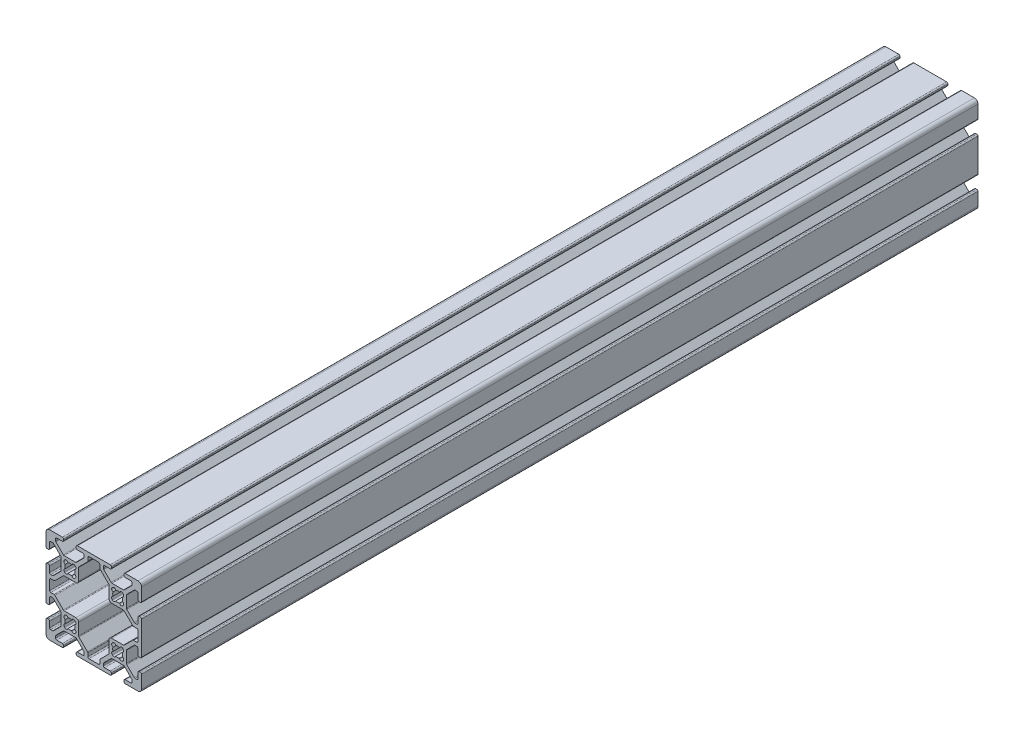
SolidWorks part; units mm, degrees
material "6105-T5 Aluminum"
ref_plane "Front Plane" through (0, 0, 0) normal (0, 0, 1) x (1, 0, 0)
ref_plane "Top Plane" through (0, 0, 0) normal (0, 1, 0) x (1, 0, 0)
ref_plane "Right Plane" through (0, 0, 0) normal (1, 0, 0) x (0, 0, -1)
sketch "Sketch1" plane through (0, 0, 0) normal (0, 0, 1) x (1, 0, 0)
  line L0 (-2.1249, 17.6955) -> (-2.3045, 17.8751)
  line L1 (-2.3045, 22.1249) -> (-2.1249, 22.3045)
  line L2 (2.1249, 22.3045) -> (2.3045, 22.1249)
  line L3 (2.3045, 17.8751) -> (2.1249, 17.6955)
  line L4 (-22.1249, 17.6955) -> (-22.3045, 17.8751)
  line L5 (-22.3045, 22.1249) -> (-22.1249, 22.3045)
  line L6 (-17.8751, 22.3045) -> (-17.6955, 22.1249)
  line L7 (-17.6955, 17.8751) -> (-17.8751, 17.6955)
  line L8 (-2.1249, -2.3045) -> (-2.3045, -2.1249)
  line L9 (-2.3045, 2.1249) -> (-2.1249, 2.3045)
  line L10 (2.1249, 2.3045) -> (2.3045, 2.1249)
  line L11 (2.3045, -2.1249) -> (2.1249, -2.3045)
  line L12 (-12.505, -7.992) -> (-12.505, -6.6448)
  line L13 (-12.6538, -6.2856) -> (-16.1962, -2.7431)
  line L14 (-16.345, -2.3839) -> (-16.345, 2.512)
  line L15 (-17.488, 3.655) -> (-22.3839, 3.655)
  line L16 (-22.7431, 3.8038) -> (-26.2856, 7.3462)
  line L17 (-26.6448, 7.495) -> (-27.992, 7.495)
  line L18 (-28.5, 8.003) -> (-28.5, 11.997)
  line L19 (-27.992, 12.505) -> (-26.6448, 12.505)
  line L20 (-26.2856, 12.6538) -> (-22.7431, 16.1962)
  line L21 (-22.3839, 16.345) -> (-17.488, 16.345)
  line L22 (-16.345, 17.488) -> (-16.345, 22.3839)
  line L23 (-16.1962, 22.7431) -> (-12.6538, 26.2856)
  line L24 (-12.505, 26.6448) -> (-12.505, 27.992)
  line L25 (-11.997, 28.5) -> (-8.003, 28.5)
  line L26 (-7.495, 27.992) -> (-7.495, 26.6448)
  line L27 (-7.3462, 26.2856) -> (-3.8038, 22.7431)
  line L28 (-3.655, 22.3839) -> (-3.655, 17.488)
  line L29 (-2.512, 16.345) -> (2.3839, 16.345)
  line L30 (2.7431, 16.1962) -> (6.2856, 12.6538)
  line L31 (6.6448, 12.505) -> (7.992, 12.505)
  line L32 (8.5, 11.997) -> (8.5, 8.003)
  line L33 (7.992, 7.495) -> (6.6448, 7.495)
  line L34 (6.2856, 7.3462) -> (2.7431, 3.8038)
  line L35 (2.3839, 3.655) -> (-2.512, 3.655)
  line L36 (-3.655, 2.512) -> (-3.655, -2.3839)
  line L37 (-3.8038, -2.7431) -> (-7.3462, -6.2856)
  line L38 (-7.495, -6.6448) -> (-7.495, -7.992)
  line L39 (-8.003, -8.5) -> (-11.997, -8.5)
  line L40 (-22.1249, -2.3045) -> (-22.3045, -2.1249)
  line L41 (-22.3045, 2.1249) -> (-22.1249, 2.3045)
  line L42 (-17.8751, 2.3045) -> (-17.6955, 2.1249)
  line L43 (-17.6955, -2.1249) -> (-17.8751, -2.3045)
  line L44 (-22.3839, -3.655) -> (-17.6161, -3.655)
  line L45 (-17.2569, -3.8038) -> (-14.1538, -6.9069)
  line L46 (-14.005, -7.2661) -> (-14.005, -7.992)
  line L47 (-14.513, -8.5) -> (-16.862, -8.5)
  line L48 (-17.37, -9.008) -> (-17.37, -9.492)
  line L49 (-16.862, -10) -> (-3.138, -10)
  line L50 (-2.63, -9.492) -> (-2.63, -9.008)
  line L51 (-3.138, -8.5) -> (-5.487, -8.5)
  line L52 (-5.995, -7.992) -> (-5.995, -7.2661)
  line L53 (-5.8462, -6.9069) -> (-2.7431, -3.8038)
  line L54 (-2.3839, -3.655) -> (2.3839, -3.655)
  line L55 (2.7431, -3.8038) -> (5.8462, -6.9069)
  line L56 (5.995, -7.2661) -> (5.995, -7.992)
  line L57 (5.487, -8.5) -> (3.138, -8.5)
  line L58 (2.63, -9.008) -> (2.63, -9.492)
  line L59 (3.138, -10) -> (8.5, -10)
  line L60 (10, -8.5) -> (10, -3.138)
  line L61 (9.492, -2.63) -> (9.008, -2.63)
  line L62 (8.5, -3.138) -> (8.5, -5.487)
  line L63 (7.992, -5.995) -> (7.2661, -5.995)
  line L64 (6.9069, -5.8462) -> (3.8038, -2.7431)
  line L65 (3.655, -2.3839) -> (3.655, 2.3839)
  line L66 (3.8038, 2.7431) -> (6.9069, 5.8462)
  line L67 (7.2661, 5.995) -> (7.992, 5.995)
  line L68 (8.5, 5.487) -> (8.5, 3.138)
  line L69 (9.008, 2.63) -> (9.492, 2.63)
  line L70 (10, 3.138) -> (10, 16.862)
  line L71 (9.492, 17.37) -> (9.008, 17.37)
  line L72 (8.5, 16.862) -> (8.5, 14.513)
  line L73 (7.992, 14.005) -> (7.2661, 14.005)
  line L74 (6.9069, 14.1538) -> (3.8038, 17.2569)
  line L75 (3.655, 17.6161) -> (3.655, 22.3839)
  line L76 (3.8038, 22.7431) -> (6.9069, 25.8462)
  line L77 (7.2661, 25.995) -> (7.992, 25.995)
  line L78 (8.5, 25.487) -> (8.5, 23.138)
  line L79 (9.008, 22.63) -> (9.492, 22.63)
  line L80 (10, 23.138) -> (10, 28.5)
  line L81 (8.5, 30) -> (3.138, 30)
  line L82 (2.63, 29.492) -> (2.63, 29.008)
  line L83 (3.138, 28.5) -> (5.487, 28.5)
  line L84 (5.995, 27.992) -> (5.995, 27.2661)
  line L85 (5.8462, 26.9069) -> (2.7431, 23.8038)
  line L86 (2.3839, 23.655) -> (-2.3839, 23.655)
  line L87 (-2.7431, 23.8038) -> (-5.8462, 26.9069)
  line L88 (-5.995, 27.2661) -> (-5.995, 27.992)
  line L89 (-5.487, 28.5) -> (-3.138, 28.5)
  line L90 (-2.63, 29.008) -> (-2.63, 29.492)
  line L91 (-3.138, 30) -> (-16.862, 30)
  line L92 (-17.37, 29.492) -> (-17.37, 29.008)
  line L93 (-16.862, 28.5) -> (-14.513, 28.5)
  line L94 (-14.005, 27.992) -> (-14.005, 27.2661)
  line L95 (-14.1538, 26.9069) -> (-17.2569, 23.8038)
  line L96 (-17.6161, 23.655) -> (-22.3839, 23.655)
  line L97 (-22.7431, 23.8038) -> (-25.8462, 26.9069)
  line L98 (-25.995, 27.2661) -> (-25.995, 27.992)
  line L99 (-25.487, 28.5) -> (-23.138, 28.5)
  line L100 (-22.63, 29.008) -> (-22.63, 29.492)
  line L101 (-23.138, 30) -> (-28.5, 30)
  line L102 (-30, 28.5) -> (-30, 23.138)
  line L103 (-29.492, 22.63) -> (-29.008, 22.63)
  line L104 (-28.5, 23.138) -> (-28.5, 25.487)
  line L105 (-27.992, 25.995) -> (-27.2661, 25.995)
  line L106 (-26.9069, 25.8462) -> (-23.8038, 22.7431)
  line L107 (-23.655, 22.3839) -> (-23.655, 17.6161)
  line L108 (-23.8038, 17.2569) -> (-26.9069, 14.1538)
  line L109 (-27.2661, 14.005) -> (-27.992, 14.005)
  line L110 (-28.5, 14.513) -> (-28.5, 16.862)
  line L111 (-29.008, 17.37) -> (-29.492, 17.37)
  line L112 (-30, 16.862) -> (-30, 3.138)
  line L113 (-29.492, 2.63) -> (-29.008, 2.63)
  line L114 (-28.5, 3.138) -> (-28.5, 5.487)
  line L115 (-27.992, 5.995) -> (-27.2661, 5.995)
  line L116 (-26.9069, 5.8462) -> (-23.8038, 2.7431)
  line L117 (-23.655, 2.3839) -> (-23.655, -2.3839)
  line L118 (-23.8038, -2.7431) -> (-26.9069, -5.8462)
  line L119 (-27.2661, -5.995) -> (-27.992, -5.995)
  line L120 (-28.5, -5.487) -> (-28.5, -3.138)
  line L121 (-29.008, -2.63) -> (-29.492, -2.63)
  line L122 (-30, -3.138) -> (-30, -8.5)
  line L123 (-28.5, -10) -> (-23.138, -10)
  line L124 (-22.63, -9.492) -> (-22.63, -9.008)
  line L125 (-23.138, -8.5) -> (-25.487, -8.5)
  line L126 (-25.995, -7.992) -> (-25.995, -7.2661)
  line L127 (-25.8462, -6.9069) -> (-22.7431, -3.8038)
  arc A0 (-1.9351, 19.196) -> (-2.3045, 17.8751) centre (-1.748, 18.4316) ccw
  arc A1 (-1.9351, 20.804) -> (-1.9351, 19.196) centre (0, 20) ccw
  arc A2 (-2.3045, 22.1249) -> (-1.9351, 20.804) centre (-1.748, 21.5684) ccw
  arc A3 (-0.804, 21.9351) -> (-2.1249, 22.3045) centre (-1.5684, 21.748) ccw
  arc A4 (0.804, 21.9351) -> (-0.804, 21.9351) centre (0, 20) ccw
  arc A5 (2.1249, 22.3045) -> (0.804, 21.9351) centre (1.5684, 21.748) ccw
  arc A6 (1.9351, 20.804) -> (2.3045, 22.1249) centre (1.748, 21.5684) ccw
  arc A7 (1.9351, 19.196) -> (1.9351, 20.804) centre (0, 20) ccw
  arc A8 (2.3045, 17.8751) -> (1.9351, 19.196) centre (1.748, 18.4316) ccw
  arc A9 (0.804, 18.0649) -> (2.1249, 17.6955) centre (1.5684, 18.252) ccw
  arc A10 (-0.804, 18.0649) -> (0.804, 18.0649) centre (0, 20) ccw
  arc A11 (-2.1249, 17.6955) -> (-0.804, 18.0649) centre (-1.5684, 18.252) ccw
  arc A12 (-21.9351, 19.196) -> (-22.3045, 17.8751) centre (-21.748, 18.4316) ccw
  arc A13 (-21.9351, 20.804) -> (-21.9351, 19.196) centre (-20, 20) ccw
  arc A14 (-22.3045, 22.1249) -> (-21.9351, 20.804) centre (-21.748, 21.5684) ccw
  arc A15 (-20.804, 21.9351) -> (-22.1249, 22.3045) centre (-21.5684, 21.748) ccw
  arc A16 (-19.196, 21.9351) -> (-20.804, 21.9351) centre (-20, 20) ccw
  arc A17 (-17.8751, 22.3045) -> (-19.196, 21.9351) centre (-18.4316, 21.748) ccw
  arc A18 (-18.0649, 20.804) -> (-17.6955, 22.1249) centre (-18.252, 21.5684) ccw
  arc A19 (-18.0649, 19.196) -> (-18.0649, 20.804) centre (-20, 20) ccw
  arc A20 (-17.6955, 17.8751) -> (-18.0649, 19.196) centre (-18.252, 18.4316) ccw
  arc A21 (-19.196, 18.0649) -> (-17.8751, 17.6955) centre (-18.4316, 18.252) ccw
  arc A22 (-20.804, 18.0649) -> (-19.196, 18.0649) centre (-20, 20) ccw
  arc A23 (-22.1249, 17.6955) -> (-20.804, 18.0649) centre (-21.5684, 18.252) ccw
  arc A24 (-1.9351, -0.804) -> (-2.3045, -2.1249) centre (-1.748, -1.5684) ccw
  arc A25 (-1.9351, 0.804) -> (-1.9351, -0.804) centre (0, 0) ccw
  arc A26 (-2.3045, 2.1249) -> (-1.9351, 0.804) centre (-1.748, 1.5684) ccw
  arc A27 (-0.804, 1.9351) -> (-2.1249, 2.3045) centre (-1.5684, 1.748) ccw
  arc A28 (0.804, 1.9351) -> (-0.804, 1.9351) centre (0, 0) ccw
  arc A29 (2.1249, 2.3045) -> (0.804, 1.9351) centre (1.5684, 1.748) ccw
  arc A30 (1.9351, 0.804) -> (2.3045, 2.1249) centre (1.748, 1.5684) ccw
  arc A31 (1.9351, -0.804) -> (1.9351, 0.804) centre (0, 0) ccw
  arc A32 (2.3045, -2.1249) -> (1.9351, -0.804) centre (1.748, -1.5684) ccw
  arc A33 (0.804, -1.9351) -> (2.1249, -2.3045) centre (1.5684, -1.748) ccw
  arc A34 (-0.804, -1.9351) -> (0.804, -1.9351) centre (0, 0) ccw
  arc A35 (-2.1249, -2.3045) -> (-0.804, -1.9351) centre (-1.5684, -1.748) ccw
  arc A36 (-12.505, -7.992) -> (-11.997, -8.5) centre (-11.997, -7.992) ccw
  arc A37 (-12.505, -6.6448) -> (-12.6538, -6.2856) centre (-13.013, -6.6448) ccw
  arc A38 (-16.345, -2.3839) -> (-16.1962, -2.7431) centre (-15.837, -2.3839) ccw
  arc A39 (-16.345, 2.512) -> (-17.488, 3.655) centre (-17.488, 2.512) ccw
  arc A40 (-22.7431, 3.8038) -> (-22.3839, 3.655) centre (-22.3839, 4.163) ccw
  arc A41 (-26.2856, 7.3462) -> (-26.6448, 7.495) centre (-26.6448, 6.987) ccw
  arc A42 (-28.5, 8.003) -> (-27.992, 7.495) centre (-27.992, 8.003) ccw
  arc A43 (-27.992, 12.505) -> (-28.5, 11.997) centre (-27.992, 11.997) ccw
  arc A44 (-26.6448, 12.505) -> (-26.2856, 12.6538) centre (-26.6448, 13.013) ccw
  arc A45 (-22.3839, 16.345) -> (-22.7431, 16.1962) centre (-22.3839, 15.837) ccw
  arc A46 (-17.488, 16.345) -> (-16.345, 17.488) centre (-17.488, 17.488) ccw
  arc A47 (-16.1962, 22.7431) -> (-16.345, 22.3839) centre (-15.837, 22.3839) ccw
  arc A48 (-12.6538, 26.2856) -> (-12.505, 26.6448) centre (-13.013, 26.6448) ccw
  arc A49 (-11.997, 28.5) -> (-12.505, 27.992) centre (-11.997, 27.992) ccw
  arc A50 (-7.495, 27.992) -> (-8.003, 28.5) centre (-8.003, 27.992) ccw
  arc A51 (-7.495, 26.6448) -> (-7.3462, 26.2856) centre (-6.987, 26.6448) ccw
  arc A52 (-3.655, 22.3839) -> (-3.8038, 22.7431) centre (-4.163, 22.3839) ccw
  arc A53 (-3.655, 17.488) -> (-2.512, 16.345) centre (-2.512, 17.488) ccw
  arc A54 (2.7431, 16.1962) -> (2.3839, 16.345) centre (2.3839, 15.837) ccw
  arc A55 (6.2856, 12.6538) -> (6.6448, 12.505) centre (6.6448, 13.013) ccw
  arc A56 (8.5, 11.997) -> (7.992, 12.505) centre (7.992, 11.997) ccw
  arc A57 (7.992, 7.495) -> (8.5, 8.003) centre (7.992, 8.003) ccw
  arc A58 (6.6448, 7.495) -> (6.2856, 7.3462) centre (6.6448, 6.987) ccw
  arc A59 (2.3839, 3.655) -> (2.7431, 3.8038) centre (2.3839, 4.163) ccw
  arc A60 (-2.512, 3.655) -> (-3.655, 2.512) centre (-2.512, 2.512) ccw
  arc A61 (-3.8038, -2.7431) -> (-3.655, -2.3839) centre (-4.163, -2.3839) ccw
  arc A62 (-7.3462, -6.2856) -> (-7.495, -6.6448) centre (-6.987, -6.6448) ccw
  arc A63 (-8.003, -8.5) -> (-7.495, -7.992) centre (-8.003, -7.992) ccw
  arc A64 (-21.9351, -0.804) -> (-22.3045, -2.1249) centre (-21.748, -1.5684) ccw
  arc A65 (-21.9351, 0.804) -> (-21.9351, -0.804) centre (-20, 0) ccw
  arc A66 (-22.3045, 2.1249) -> (-21.9351, 0.804) centre (-21.748, 1.5684) ccw
  arc A67 (-20.804, 1.9351) -> (-22.1249, 2.3045) centre (-21.5684, 1.748) ccw
  arc A68 (-19.196, 1.9351) -> (-20.804, 1.9351) centre (-20, 0) ccw
  arc A69 (-17.8751, 2.3045) -> (-19.196, 1.9351) centre (-18.4316, 1.748) ccw
  arc A70 (-18.0649, 0.804) -> (-17.6955, 2.1249) centre (-18.252, 1.5684) ccw
  arc A71 (-18.0649, -0.804) -> (-18.0649, 0.804) centre (-20, 0) ccw
  arc A72 (-17.6955, -2.1249) -> (-18.0649, -0.804) centre (-18.252, -1.5684) ccw
  arc A73 (-19.196, -1.9351) -> (-17.8751, -2.3045) centre (-18.4316, -1.748) ccw
  arc A74 (-20.804, -1.9351) -> (-19.196, -1.9351) centre (-20, 0) ccw
  arc A75 (-22.1249, -2.3045) -> (-20.804, -1.9351) centre (-21.5684, -1.748) ccw
  arc A76 (-22.3839, -3.655) -> (-22.7431, -3.8038) centre (-22.3839, -4.163) ccw
  arc A77 (-17.2569, -3.8038) -> (-17.6161, -3.655) centre (-17.6161, -4.163) ccw
  arc A78 (-14.005, -7.2661) -> (-14.1538, -6.9069) centre (-14.513, -7.2661) ccw
  arc A79 (-14.513, -8.5) -> (-14.005, -7.992) centre (-14.513, -7.992) ccw
  arc A80 (-16.862, -8.5) -> (-17.37, -9.008) centre (-16.862, -9.008) ccw
  arc A81 (-17.37, -9.492) -> (-16.862, -10) centre (-16.862, -9.492) ccw
  arc A82 (-3.138, -10) -> (-2.63, -9.492) centre (-3.138, -9.492) ccw
  arc A83 (-2.63, -9.008) -> (-3.138, -8.5) centre (-3.138, -9.008) ccw
  arc A84 (-5.995, -7.992) -> (-5.487, -8.5) centre (-5.487, -7.992) ccw
  arc A85 (-5.8462, -6.9069) -> (-5.995, -7.2661) centre (-5.487, -7.2661) ccw
  arc A86 (-2.3839, -3.655) -> (-2.7431, -3.8038) centre (-2.3839, -4.163) ccw
  arc A87 (2.7431, -3.8038) -> (2.3839, -3.655) centre (2.3839, -4.163) ccw
  arc A88 (5.995, -7.2661) -> (5.8462, -6.9069) centre (5.487, -7.2661) ccw
  arc A89 (5.487, -8.5) -> (5.995, -7.992) centre (5.487, -7.992) ccw
  arc A90 (3.138, -8.5) -> (2.63, -9.008) centre (3.138, -9.008) ccw
  arc A91 (2.63, -9.492) -> (3.138, -10) centre (3.138, -9.492) ccw
  arc A92 (8.5, -10) -> (10, -8.5) centre (8.5, -8.5) ccw
  arc A93 (10, -3.138) -> (9.492, -2.63) centre (9.492, -3.138) ccw
  arc A94 (9.008, -2.63) -> (8.5, -3.138) centre (9.008, -3.138) ccw
  arc A95 (7.992, -5.995) -> (8.5, -5.487) centre (7.992, -5.487) ccw
  arc A96 (6.9069, -5.8462) -> (7.2661, -5.995) centre (7.2661, -5.487) ccw
  arc A97 (3.655, -2.3839) -> (3.8038, -2.7431) centre (4.163, -2.3839) ccw
  arc A98 (3.8038, 2.7431) -> (3.655, 2.3839) centre (4.163, 2.3839) ccw
  arc A99 (7.2661, 5.995) -> (6.9069, 5.8462) centre (7.2661, 5.487) ccw
  arc A100 (8.5, 5.487) -> (7.992, 5.995) centre (7.992, 5.487) ccw
  arc A101 (8.5, 3.138) -> (9.008, 2.63) centre (9.008, 3.138) ccw
  arc A102 (9.492, 2.63) -> (10, 3.138) centre (9.492, 3.138) ccw
  arc A103 (10, 16.862) -> (9.492, 17.37) centre (9.492, 16.862) ccw
  arc A104 (9.008, 17.37) -> (8.5, 16.862) centre (9.008, 16.862) ccw
  arc A105 (7.992, 14.005) -> (8.5, 14.513) centre (7.992, 14.513) ccw
  arc A106 (6.9069, 14.1538) -> (7.2661, 14.005) centre (7.2661, 14.513) ccw
  arc A107 (3.655, 17.6161) -> (3.8038, 17.2569) centre (4.163, 17.6161) ccw
  arc A108 (3.8038, 22.7431) -> (3.655, 22.3839) centre (4.163, 22.3839) ccw
  arc A109 (7.2661, 25.995) -> (6.9069, 25.8462) centre (7.2661, 25.487) ccw
  arc A110 (8.5, 25.487) -> (7.992, 25.995) centre (7.992, 25.487) ccw
  arc A111 (8.5, 23.138) -> (9.008, 22.63) centre (9.008, 23.138) ccw
  arc A112 (9.492, 22.63) -> (10, 23.138) centre (9.492, 23.138) ccw
  arc A113 (10, 28.5) -> (8.5, 30) centre (8.5, 28.5) ccw
  arc A114 (3.138, 30) -> (2.63, 29.492) centre (3.138, 29.492) ccw
  arc A115 (2.63, 29.008) -> (3.138, 28.5) centre (3.138, 29.008) ccw
  arc A116 (5.995, 27.992) -> (5.487, 28.5) centre (5.487, 27.992) ccw
  arc A117 (5.8462, 26.9069) -> (5.995, 27.2661) centre (5.487, 27.2661) ccw
  arc A118 (2.3839, 23.655) -> (2.7431, 23.8038) centre (2.3839, 24.163) ccw
  arc A119 (-2.7431, 23.8038) -> (-2.3839, 23.655) centre (-2.3839, 24.163) ccw
  arc A120 (-5.995, 27.2661) -> (-5.8462, 26.9069) centre (-5.487, 27.2661) ccw
  arc A121 (-5.487, 28.5) -> (-5.995, 27.992) centre (-5.487, 27.992) ccw
  arc A122 (-3.138, 28.5) -> (-2.63, 29.008) centre (-3.138, 29.008) ccw
  arc A123 (-2.63, 29.492) -> (-3.138, 30) centre (-3.138, 29.492) ccw
  arc A124 (-16.862, 30) -> (-17.37, 29.492) centre (-16.862, 29.492) ccw
  arc A125 (-17.37, 29.008) -> (-16.862, 28.5) centre (-16.862, 29.008) ccw
  arc A126 (-14.005, 27.992) -> (-14.513, 28.5) centre (-14.513, 27.992) ccw
  arc A127 (-14.1538, 26.9069) -> (-14.005, 27.2661) centre (-14.513, 27.2661) ccw
  arc A128 (-17.6161, 23.655) -> (-17.2569, 23.8038) centre (-17.6161, 24.163) ccw
  arc A129 (-22.7431, 23.8038) -> (-22.3839, 23.655) centre (-22.3839, 24.163) ccw
  arc A130 (-25.995, 27.2661) -> (-25.8462, 26.9069) centre (-25.487, 27.2661) ccw
  arc A131 (-25.487, 28.5) -> (-25.995, 27.992) centre (-25.487, 27.992) ccw
  arc A132 (-23.138, 28.5) -> (-22.63, 29.008) centre (-23.138, 29.008) ccw
  arc A133 (-22.63, 29.492) -> (-23.138, 30) centre (-23.138, 29.492) ccw
  arc A134 (-28.5, 30) -> (-30, 28.5) centre (-28.5, 28.5) ccw
  arc A135 (-30, 23.138) -> (-29.492, 22.63) centre (-29.492, 23.138) ccw
  arc A136 (-29.008, 22.63) -> (-28.5, 23.138) centre (-29.008, 23.138) ccw
  arc A137 (-27.992, 25.995) -> (-28.5, 25.487) centre (-27.992, 25.487) ccw
  arc A138 (-26.9069, 25.8462) -> (-27.2661, 25.995) centre (-27.2661, 25.487) ccw
  arc A139 (-23.655, 22.3839) -> (-23.8038, 22.7431) centre (-24.163, 22.3839) ccw
  arc A140 (-23.8038, 17.2569) -> (-23.655, 17.6161) centre (-24.163, 17.6161) ccw
  arc A141 (-27.2661, 14.005) -> (-26.9069, 14.1538) centre (-27.2661, 14.513) ccw
  arc A142 (-28.5, 14.513) -> (-27.992, 14.005) centre (-27.992, 14.513) ccw
  arc A143 (-28.5, 16.862) -> (-29.008, 17.37) centre (-29.008, 16.862) ccw
  arc A144 (-29.492, 17.37) -> (-30, 16.862) centre (-29.492, 16.862) ccw
  arc A145 (-30, 3.138) -> (-29.492, 2.63) centre (-29.492, 3.138) ccw
  arc A146 (-29.008, 2.63) -> (-28.5, 3.138) centre (-29.008, 3.138) ccw
  arc A147 (-27.992, 5.995) -> (-28.5, 5.487) centre (-27.992, 5.487) ccw
  arc A148 (-26.9069, 5.8462) -> (-27.2661, 5.995) centre (-27.2661, 5.487) ccw
  arc A149 (-23.655, 2.3839) -> (-23.8038, 2.7431) centre (-24.163, 2.3839) ccw
  arc A150 (-23.8038, -2.7431) -> (-23.655, -2.3839) centre (-24.163, -2.3839) ccw
  arc A151 (-27.2661, -5.995) -> (-26.9069, -5.8462) centre (-27.2661, -5.487) ccw
  arc A152 (-28.5, -5.487) -> (-27.992, -5.995) centre (-27.992, -5.487) ccw
  arc A153 (-28.5, -3.138) -> (-29.008, -2.63) centre (-29.008, -3.138) ccw
  arc A154 (-29.492, -2.63) -> (-30, -3.138) centre (-29.492, -3.138) ccw
  arc A155 (-30, -8.5) -> (-28.5, -10) centre (-28.5, -8.5) ccw
  arc A156 (-23.138, -10) -> (-22.63, -9.492) centre (-23.138, -9.492) ccw
  arc A157 (-22.63, -9.008) -> (-23.138, -8.5) centre (-23.138, -9.008) ccw
  arc A158 (-25.995, -7.992) -> (-25.487, -8.5) centre (-25.487, -7.992) ccw
  arc A159 (-25.8462, -6.9069) -> (-25.995, -7.2661) centre (-25.487, -7.2661) ccw
extrude "Extrude1" add sketch "Sketch1" against normal blind 350
